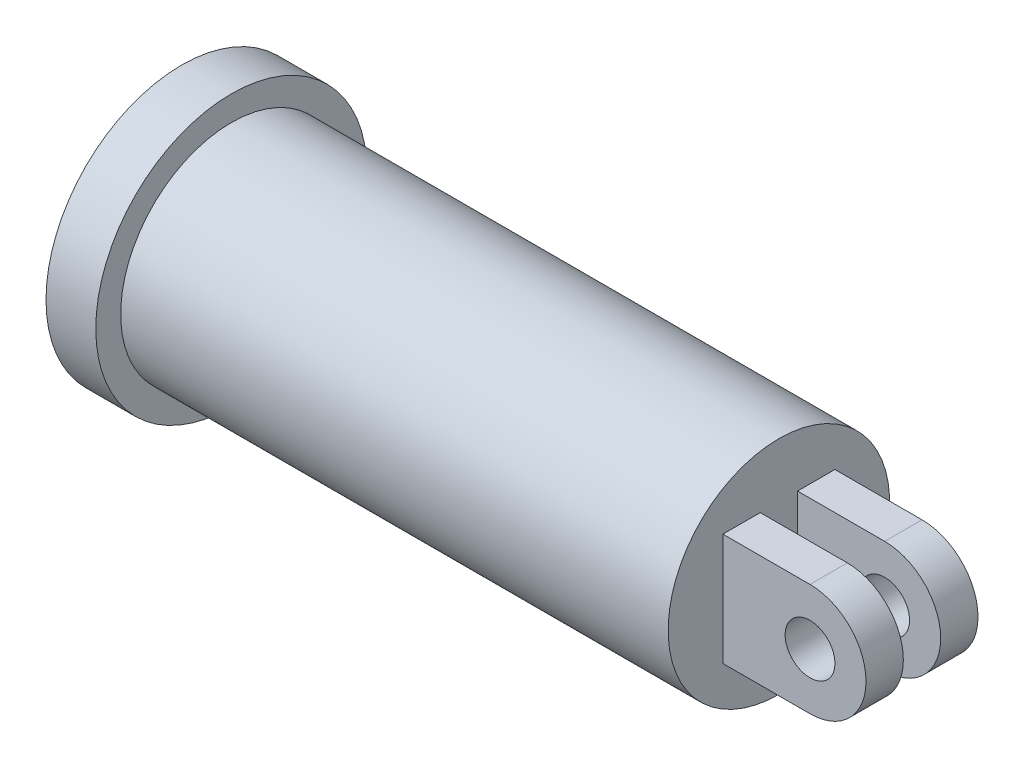
SolidWorks part; units mm, degrees
ref_plane "Front Plane" through (0, 0, 0) normal (0, 0, 1) x (1, 0, 0)
ref_plane "Top Plane" through (0, 0, 0) normal (0, 1, 0) x (1, 0, 0)
ref_plane "Right Plane" through (0, 0, 0) normal (1, 0, 0) x (0, 0, -1)
sketch "Sketch2" plane through (0, 0, 0) normal (0, 0, 1) x (1, 0, 0)
  line L0 (-120, 0) -> (120, 0)
  line L1 (120, 0) -> (120, 44.5)
  line L2 (120, 44.5) -> (-100, 44.5)
  line L3 (-100, 44.5) -> (-100, 54.5)
  line L4 (-100, 54.5) -> (-120, 54.5)
  line L5 (-120, 54.5) -> (-120, 0)
  point P3 (0, 0)
  dimension "D1" = 44.5
  dimension "D2" = 54.5
  dimension "D3" = 20
  dimension "D4" = 240
revolve "Revolve1" add sketch "Sketch2" angle 360 about L0
ref_plane "Plane1" through (0, 0, 7.5) normal (0, 0, 1) x (1, 0, 0)
sketch "Sketch3" plane through (0, 0, 7.5) normal (0, 0, 1) x (1, 0, 0)
  line L0 (120, 22.5) -> (155, 22.5)
  line L1 (120, -44.5) -> (120, 44.5) construction
  line L2 (120, -22.5) -> (155, -22.5)
  line L3 (155, 22.5) -> (155, -22.5) construction
  line L4 (120, 22.5) -> (120, -22.5)
  arc A0 (155, 22.5) -> (155, -22.5) centre (155, 0) cw
  circle A1 centre (155, 0) radius 10
  point P7 (120, 0)
  dimension "D3" = 20
  dimension "D4" = 22.5
  dimension "D1" = 45
  dimension "D2" = 35
extrude "Boss-Extrude1" add sketch "Sketch3" along normal blind 15
mirror "Mirror1" about plane through (0, 0, 0) normal (0, 0, 1) of "Boss-Extrude1"
